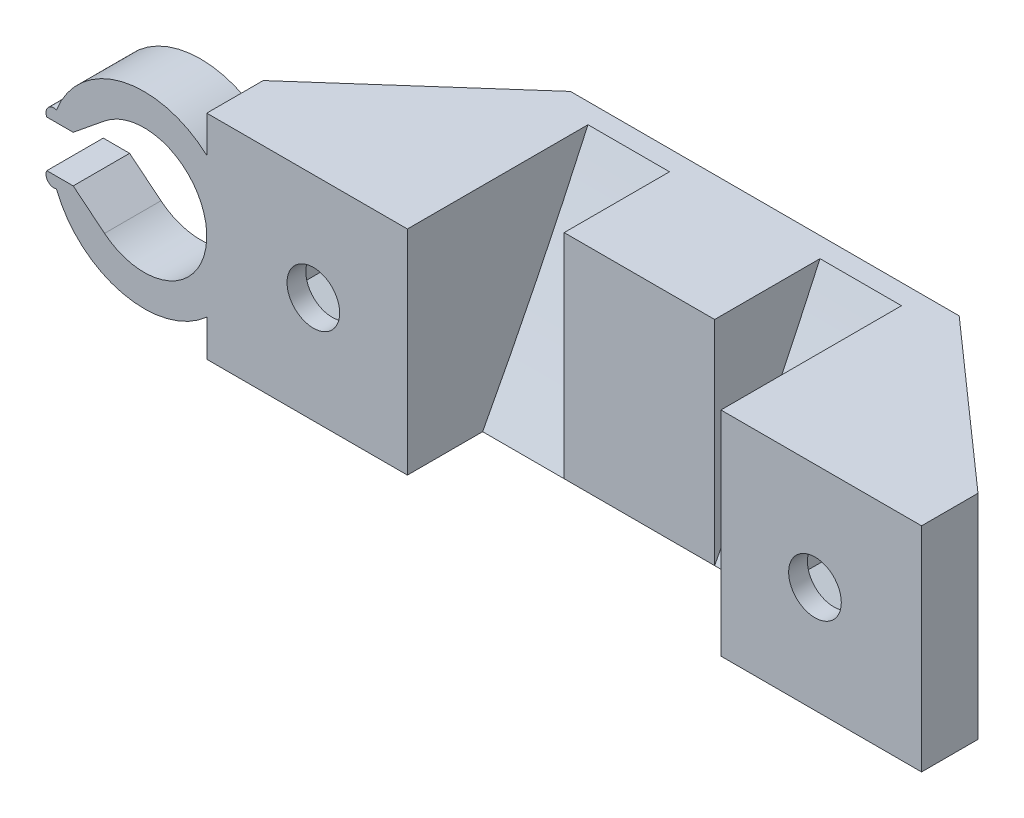
SolidWorks part; units mm, degrees
ref_plane "Front Plane" through (0, 0, 0) normal (0, 0, 1) x (1, 0, 0)
ref_plane "Top Plane" through (0, 0, 0) normal (0, 1, 0) x (1, 0, 0)
ref_plane "Right Plane" through (0, 0, 0) normal (1, 0, 0) x (0, 0, -1)
sketch "Sketch1" plane through (0, 0, 0) normal (0, 1, 0) x (1, 0, 0)
  line L0 (-27.5827, 44.1851) -> (-2.5827, 44.1851)
  line L1 (-30.5827, 54.1851) -> (0.4173, 54.1851)
  line L2 (-30.5827, 54.1851) -> (-30.5827, 42.6851)
  line L3 (-27.5827, 44.1851) -> (-27.5827, 38.1851)
  line L4 (-2.5827, 44.1851) -> (-2.5827, 38.1851)
  line L5 (-2.5827, 38.1851) -> (13.4173, 38.1851)
  line L6 (0.4173, 42.6851) -> (0.4173, 54.1851)
  line L7 (-27.5827, 38.1851) -> (-43.5827, 38.1851)
  line L8 (-43.5827, 38.1851) -> (-43.5827, 42.6851)
  line L9 (-43.5827, 42.6851) -> (-30.5827, 42.6851)
  line L10 (13.4173, 38.1851) -> (13.4173, 42.6851)
  line L11 (13.4173, 42.6851) -> (0.4173, 42.6851)
  dimension "D1" = 10
  dimension "D2" = 25
  dimension "D3" = 31
  dimension "D4" = 3
extrude "Boss-Extrude1" add sketch "Sketch1" along normal blind 17
sketch "Sketch2" plane through (0, 17, 0) normal (0, 1, 0) x (1, 0, 0)
  line L0 (-43.5827, 42.6851) -> (-30.5827, 54.1851)
  line L2 (-30.5827, 54.1851) -> (-30.5827, 42.6851) construction
  line L3 (-30.5827, 42.6851) -> (-43.5827, 42.6851)
  line L4 (0.4173, 42.6851) -> (13.4173, 42.6851)
  line L5 (-30.5827, 54.1851) -> (-30.5827, 42.6851)
  line L7 (0.4173, 42.6851) -> (0.4173, 54.1851)
  line L8 (0.4173, 54.1851) -> (13.4173, 42.6851)
extrude "Boss-Extrude2" add sketch "Sketch2" against normal blind 2
sketch "Sketch3" plane through (0, 0, 0) normal (0, -1, 0) x (1, 0, 0)
  line L0 (-43.5827, -42.6851) -> (-30.5827, -54.1851)
  line L1 (-30.5827, -54.1851) -> (-30.5827, -42.6851)
  line L2 (-30.5827, -42.6851) -> (-43.5827, -42.6851)
  line L3 (0.4173, -42.6851) -> (0.4173, -54.1851)
  line L4 (13.4173, -42.6851) -> (0.4173, -42.6851)
  line L5 (13.4173, -42.6851) -> (0.4173, -54.1851) construction
  line L6 (0.4173, -54.1851) -> (13.4173, -42.6851)
extrude "Boss-Extrude3" add sketch "Sketch3" against normal blind 2
sketch "Sketch4" plane through (0, 0, -38.1851) normal (0, 0, 1) x (1, 0, 0)
  line L0 (-27.5827, 17) -> (-27.5827, 0) construction
  line L1 (-2.5827, 17) -> (-2.5827, 0) construction
  line L2 (-27.5827, 17) -> (-27.5827, 0) construction
  circle A0 centre (-35.0827, 8.5) radius 2.1
  circle A1 centre (4.9173, 8.5) radius 2.1
  point P6 (-2.5827, 8.5)
  dimension "D1" = 7.5
  dimension "D2" = 7.5
extrude "Cut-Extrude1" cut sketch "Sketch4" against normal blind 100
sketch "Sketch5" plane through (0, 0, -42.6851) normal (0, 0, -1) x (-1, 0, 0)
  line L1 (31.5827, 6.4793) -> (31.5827, 10.5207)
  line L2 (35.0827, 4.4585) -> (31.5827, 6.4793)
  line L3 (38.5827, 6.4793) -> (35.0827, 4.4585)
  line L4 (38.5827, 10.5207) -> (38.5827, 6.4793)
  line L5 (35.0827, 12.5415) -> (38.5827, 10.5207)
  line L6 (31.5827, 10.5207) -> (35.0827, 12.5415)
  line L7 (-1.4173, 10.5207) -> (-4.9173, 12.5415)
  line L8 (-4.9173, 12.5415) -> (-8.4173, 10.5207)
  line L9 (-8.4173, 10.5207) -> (-8.4173, 6.4793)
  line L10 (-8.4173, 6.4793) -> (-4.9173, 4.4585)
  line L11 (-4.9173, 4.4585) -> (-1.4173, 6.4793)
  line L12 (-1.4173, 6.4793) -> (-1.4173, 10.5207)
  circle A0 centre (35.0827, 8.5) radius 3.5 construction
  circle A1 centre (-4.9173, 8.5) radius 3.5 construction
extrude "Cut-Extrude2" cut sketch "Sketch5" against normal blind 3
sketch "Sketch7" plane through (-2.5827, 0, 0) normal (-1, 0, 0) x (0, 0, 1)
  line L0 (-53.602, 19.278) -> (-35.3664, 18.1473)
  line L1 (-35.3664, 18.1473) -> (-35.3664, -6.2911)
  line L2 (-35.3664, -6.2911) -> (-39.3476, -8.6203)
  line L49 (24.9238, -124.4) -> (24.9238, -144.9)
  line L50 (24.9238, -144.9) -> (32.4238, -152.4)
  line L51 (32.4238, -152.4) -> (44.9238, -152.4)
  line L52 (44.9238, -152.4) -> (44.9238, -156.4)
  line L53 (44.9238, -156.4) -> (74.9238, -156.4)
  line L54 (74.9238, -156.4) -> (74.9238, -152.4)
  line L55 (74.9238, -152.4) -> (78.8238, -152.4)
  line L56 (78.8238, -152.4) -> (78.8238, -142.4)
  line L57 (78.8238, -142.4) -> (76.4238, -142.4)
  line L58 (76.4238, -142.4) -> (76.4238, -141.4)
  line L59 (76.4238, -141.4) -> (77.1738, -141.4)
  line L60 (77.1738, -141.4) -> (77.1738, -138.9)
  line L61 (77.1738, -138.9) -> (78.8238, -138.9)
  line L62 (78.8238, -138.9) -> (78.8238, -135.4)
  line L63 (78.8238, -135.4) -> (83.0238, -135.4)
  line L64 (83.0238, -135.4) -> (83.0238, -138.9)
  line L65 (83.0238, -138.9) -> (84.6738, -138.9)
  line L66 (84.6738, -138.9) -> (84.6738, -141.4)
  line L67 (84.6738, -141.4) -> (85.4238, -141.4)
  line L68 (85.4238, -141.4) -> (85.4238, -142.4)
  line L69 (85.4238, -142.4) -> (83.0238, -142.4)
  line L70 (83.0238, -142.4) -> (83.0238, -152.4)
  line L71 (83.0238, -152.4) -> (86.9238, -152.4)
  line L72 (86.9238, -152.4) -> (86.9238, -156.4)
  line L73 (86.9238, -156.4) -> (111.9238, -156.4)
  line L74 (111.9238, -156.4) -> (111.9238, -112.4)
  line L75 (-60.0762, 162.6) -> (-75.0762, 162.6)
  line L76 (29.9238, -87.4) -> (29.9238, -92.4)
  line L77 (29.9238, -92.4) -> (24.9238, -92.4)
  line L78 (24.9238, -92.4) -> (24.9238, -96.3)
  line L79 (24.9238, -96.3) -> (34.9238, -96.3)
  line L80 (34.9238, -96.3) -> (34.9238, -93.9)
  line L81 (34.9238, -93.9) -> (35.9238, -93.9)
  line L82 (35.9238, -93.9) -> (35.9238, -94.65)
  line L83 (35.9238, -94.65) -> (38.4238, -94.65)
  line L84 (38.4238, -94.65) -> (38.4238, -96.3)
  line L85 (38.4238, -96.3) -> (41.9238, -96.3)
  line L86 (41.9238, -96.3) -> (41.9238, -100.5)
  line L87 (41.9238, -100.5) -> (38.4238, -100.5)
  line L88 (38.4238, -100.5) -> (38.4238, -102.15)
  line L89 (38.4238, -102.15) -> (35.9238, -102.15)
  line L90 (35.9238, -102.15) -> (35.9238, -102.9)
  line L91 (35.9238, -102.9) -> (34.9238, -102.9)
  line L92 (34.9238, -102.9) -> (34.9238, -100.5)
  line L93 (34.9238, -100.5) -> (24.9238, -100.5)
  line L94 (24.9238, -100.5) -> (24.9238, -104.4)
  line L95 (24.9238, -104.4) -> (20.9238, -104.4)
  line L96 (20.9238, -104.4) -> (20.9238, -124.4)
  line L97 (20.9238, -124.4) -> (24.9238, -124.4)
  arc A3 (111.9238, -112.4) -> (105.4733, -97.6891) centre (91.9238, -112.4) ccw
  arc A4 (-60.0762, 162.6) -> (105.4733, -97.6891) centre (511.9603, 343.6365) ccw
  arc A5 (-75.0762, 162.6) -> (29.9238, -87.4) centre (198.0141, 130.248) ccw
  arc A8 (-53.602, 19.278) -> (-39.3476, -8.6203) centre (198.0141, 130.248) ccw
  dimension "D1" = 0
extrude "Cut-Extrude3" cut sketch "Sketch7" along normal blind 6.5
sketch "Sketch8" plane through (-27.5827, 0, 0) normal (1, 0, 0) x (0, 0, -1)
  line L0 (60.1332, 35.4591) -> (29.9453, 35.4591)
  line L1 (29.9453, 35.4591) -> (34.1961, -17.0728)
  arc A0 (-29.9238, -87.4) -> (75.0762, 162.6) centre (-198.0141, 130.248) ccw construction
  arc A1 (34.1961, -17.0728) -> (60.1332, 35.4591) centre (-198.0141, 130.248) ccw
extrude "Cut-Extrude4" cut sketch "Sketch8" along normal blind 6.5
sketch "Sketch9" plane through (0, 0, -38.1851) normal (0, 0, 1) x (1, 0, 0)
  line L0 (-51.7367, 12.3797) -> (-54.2333, 10.35)
  line L1 (-43.5827, 0) -> (-27.5827, 0) construction
  line L2 (-43.5827, 17) -> (-43.5827, 0) construction
  line L3 (-56.3367, 6.65) -> (-54.2333, 6.65)
  line L4 (-56.3367, 10.35) -> (-54.2333, 10.35)
  line L6 (-51.7367, 4.6203) -> (-54.2333, 6.65)
  arc A0 (-51.7367, 4.6203) -> (-51.7367, 12.3797) centre (-48.5827, 8.5) ccw
  arc A2 (-55.5695, 11.2266) -> (-56.3367, 10.35) centre (-55.7735, 10.6312) ccw
  arc A3 (-55.5695, 5.7734) -> (-56.3367, 6.65) centre (-55.7735, 6.3688) cw
  arc A5 (-55.5695, 5.7734) -> (-55.5695, 11.2266) centre (-48.5827, 8.5) ccw
  dimension "D1" = 8.5
  dimension "D2" = 5
extrude "Boss-Extrude4" add sketch "Sketch9" against normal blind 4.5
